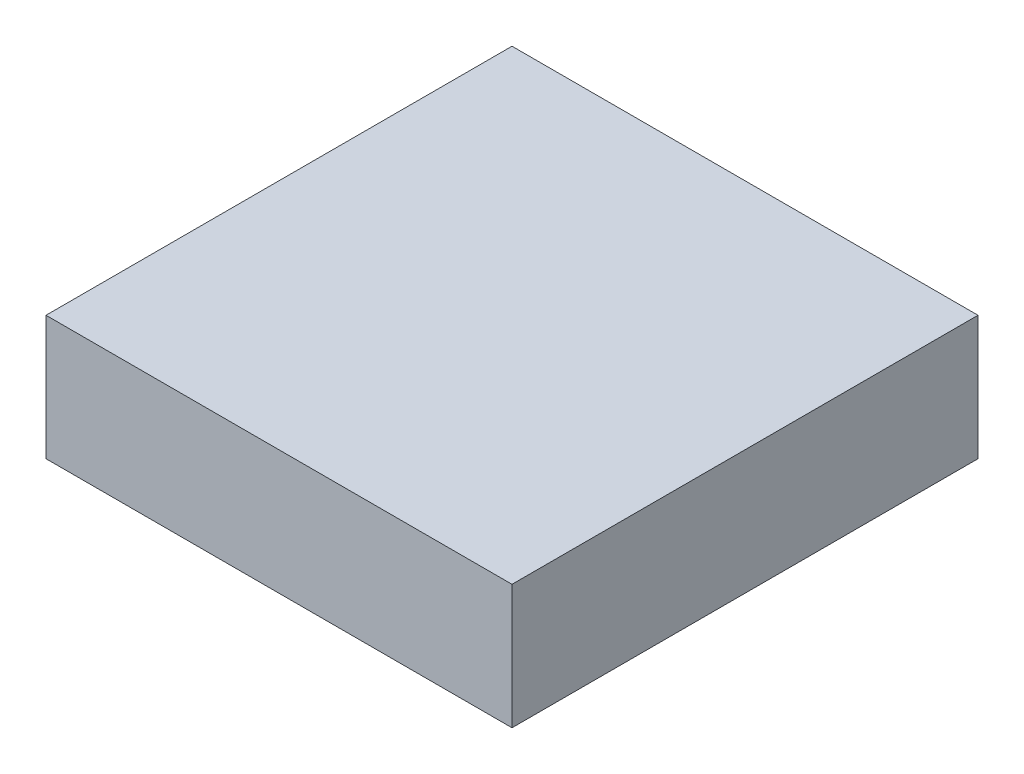
SolidWorks part; units mm, degrees
ref_plane "Front Plane" through (0, 0, 0) normal (0, 0, 1) x (1, 0, 0)
ref_plane "Top Plane" through (0, 0, 0) normal (0, 1, 0) x (1, 0, 0)
ref_plane "Right Plane" through (0, 0, 0) normal (1, 0, 0) x (0, 0, -1)
sketch "Sketch1" plane through (0, 0, 0) normal (0, 1, 0) x (1, 0, 0)
  line L1 (0, 3) -> (3, 3)
  line L2 (0, 3) -> (0, 0)
  line L3 (0, 0) -> (3, 0)
  line L4 (3, 3) -> (3, 0)
  dimension "D1" = 3
  dimension "D2" = 3
extrude "Boss-Extrude1" add sketch "Sketch1" along normal blind 0.8
sketch "Sketch2" plane through (0, 0.8, 0) normal (0, 1, 0) x (1, 0, 0)
  line L0 (0, 0) -> (3, 0) construction
  line L1 (1, 2) -> (2, 2)
  line L2 (1, 2) -> (1, 1)
  line L3 (1, 1) -> (2, 1)
  line L4 (2, 2) -> (2, 1)
  line L5 (3, 0) -> (3, 3) construction
  line L6 (3, 1.5) -> (0, 1.5)
  line L7 (0, 3) -> (0, 0) construction
  point P6 (1.5, 0)
  point P7 (1.5, 1)
  point P10 (3, 1.5)
  point P11 (2, 1.5)
  dimension "D1" = 1
  dimension "D2" = 1
